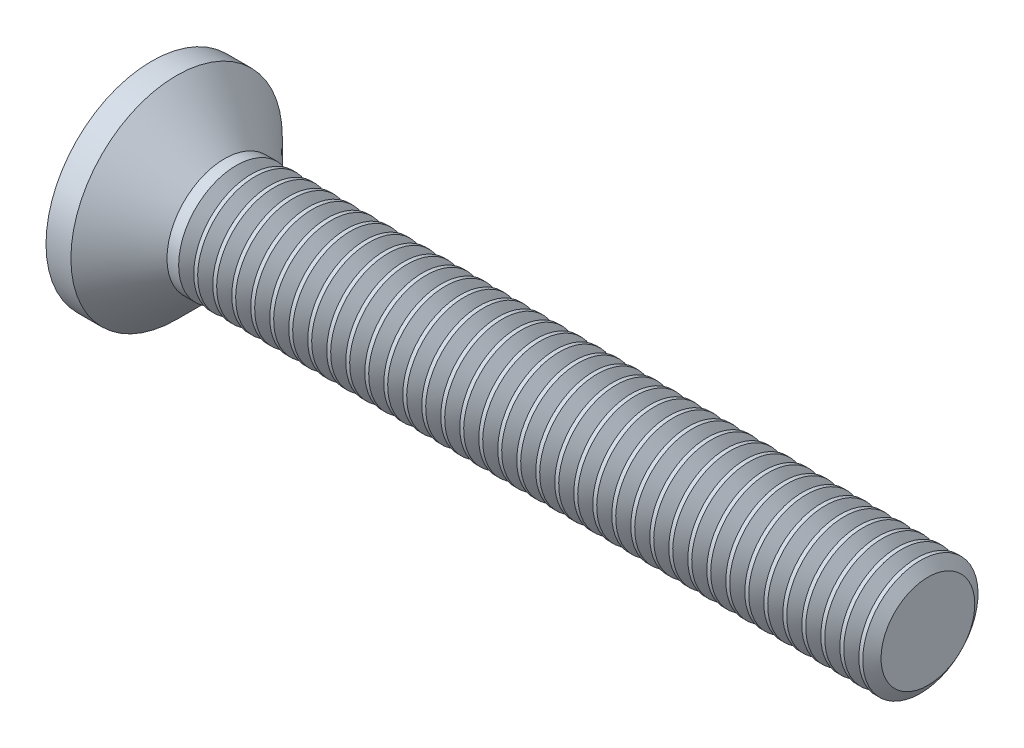
SolidWorks part; units mm, degrees
revolve "Base-Revolve" add sketch "BodySke" angle 360 about L4
sketch "BodySke" plane through (0, 0, 0) normal (0, 0, 1) x (1, 0, 0)
  line L0 (0, 0) -> (20.7277, 0)
  line L1 (20.7277, 0) -> (20.7277, 1.5)
  line L2 (20.7277, 1.5) -> (2.4277, 1.5)
  line L3 (2.4277, 1.5) -> (-7.1953, 11.123) construction
  line L4 (-15.875, 0) -> (82.55, 0) construction
  line L5 (2.4277, -1.5) -> (-7.1953, -11.123) construction
  line L6 (2.9277, 4.675) -> (2.9277, -11.2) construction
  line L7 (0.7277, 8.7375) -> (0.7277, -7.1375) construction
  line L8 (2.4277, 1.5) -> (1.1777, 2.75)
  line L9 (1.1777, 2.75) -> (0.53, 2.75)
  arc A0 (0, 0) -> (0.53, 2.75) centre (7.4, 0) cw
  arc A1 (0.7277, 3.2) -> (0, 0) centre (7.4, 0) ccw construction
  dimension "Crown_rad" = 7.4
  dimension "Diameter" = 3
  dimension "Advance" = 0.5
  dimension "Thread_nom" = 20
  dimension "Head_ang" = 90
  dimension "D3" = 6.4
  dimension "Side_ht" = 1.7
  dimension "D4" = 0.7277
  dimension "Length" = 20
  dimension "Head_dia" = 5.5
cosmetic thread "ThreadCosmetic" [suppressed] parameters "Thread_length"=17.8, "Thread_minor"=2.439
ref_plane "Plane1" through (0, 0, 0) normal (0, 0, 1) x (1, 0, 0)
ref_plane "Plane2" through (0, 0, 0) normal (0, 1, 0) x (1, 0, 0)
ref_plane "Plane3" through (0, 0, 0) normal (1, 0, 0) x (0, 0, -1)
sketch "Sketch2" plane through (0, 0, 0) normal (1, 0, 0) x (0, 0, -1)
  line L0 (2.75, -0.5) -> (-2.75, -0.5)
  line L1 (2.75, -0.5) -> (2.75, 0.5)
  line L2 (-2.75, 0.5) -> (2.75, 0.5)
  line L3 (-2.75, 0.5) -> (-2.75, -0.5)
  dimension "D1" = 5.5
  dimension "Slot_width" = 1
  dimension "D3" = 2.75
  dimension "D4" = 0.5
extrude "Slot" [suppressed] cut sketch "Sketch2" along normal blind 1.5
sketch "Sketch3" plane through (0, 0, 0) normal (1, 0, 0) x (0, 0, -1)
  line L0 (0.415, -1.72) -> (-0.415, -1.72)
  line L1 (0.415, -1.72) -> (0.415, 1.72)
  line L2 (-0.415, 1.72) -> (0.415, 1.72)
  line L3 (-0.415, 1.72) -> (-0.415, -1.72)
  dimension "Cross_width" = 0.83
  dimension "D1" = 0.415
  dimension "Cross_dia" = 3.44
  dimension "D2" = 1.72
ref_plane "Plane4" through (2.33, 0, 0) normal (1, 0, 0) x (0, 0, -1)
sketch "Sketch4" plane through (2.33, 0, 0) normal (1, 0, 0) x (0, 0, -1)
  line L0 (0.2075, -0.2075) -> (-0.2075, -0.2075)
  line L1 (0.2075, -0.2075) -> (0.2075, 0.2075)
  line L2 (-0.2075, 0.2075) -> (0.2075, 0.2075)
  line L3 (-0.2075, 0.2075) -> (-0.2075, -0.2075)
  dimension "D1" = 0.415
  dimension "D2" = 0.415
  dimension "D3" = 0.2075
  dimension "D4" = 0.2075
loft "Cross" cut profiles "Sketch3", "Sketch4"
pattern_circular "CirPattern1" count 2 every 90 about axis through (0, 0, 0) along (1, 0, 0) of "Cross"
sketch "ThdSchSke" plane through (0, 0, 0) normal (0, 0, 1) x (1, 0, 0)
  line L0 (2.9277, -1.2195) -> (2.7313, -1.5)
  line L1 (2.9277, -1.2195) -> (3.1241, -1.5)
  line L2 (3.1241, -1.5) -> (3.1241, -1.875)
  line L3 (-3.175, 0) -> (5.1513, 0) construction
  line L5 (3.1241, -1.875) -> (2.7313, -1.875)
  line L6 (2.7313, -1.875) -> (2.7313, -1.5)
  line L8 (20.7277, -1.5) -> (20.7277, 1.5) construction
  dimension "Diameter" = 3
  dimension "Thread_minor" = 2.439
  dimension "Start" = 17.8
revolve "ThreadSchematic" cut sketch "ThdSchSke" angle 360 about L3
pattern_linear "ThdSchPat" count 37 spacing 0.4944 along (1, 0, 0) of "ThreadSchematic"
equation "\"D1@Sketch2\" = \"Head_dia@BodySke\""
equation "\"D3@Sketch2\" = \"D1@Sketch2\" / 2"
equation "\"D4@Sketch2\" = \"Slot_width@Sketch2\" / 2"
equation "\"D1@Sketch3\" = \"Cross_width@Sketch3\" / 2"
equation "\"D2@Sketch3\" = \"Cross_dia@Sketch3\" / 2"
equation "\"D1@Sketch4\" = \"Cross_width@Sketch3\"*.5"
equation "\"D2@Sketch4\" = \"D1@Sketch4\""
equation "\"D3@Sketch4\" = \"D1@Sketch4\" / 2"
equation "\"D4@Sketch4\" = \"D2@Sketch4\" / 2"
equation "\"Thread_length@ThreadCosmetic\" = ((sgn( (\"Length@BodySke\" - \"Advance@BodySke\" - \"Side_ht@BodySke\" ) - \"Thread_nom@BodySke\" )-1)*( (\"Length@BodySke\" - \"Advance@BodySke\" - \"Side_ht@BodySke\" ) - \"Thread_nom@BodySke\" ))/-2+ \"Thread_nom@BodySke\""
equation "\"Thread_minor@ThdSchSke\" = \"Thread_minor@ThreadCosmetic\""
equation "\"Diameter@ThdSchSke\" = \"Diameter@BodySke\""
equation "\"Overcut@ThdSchSke\" = \"Diameter@BodySke\" * 1.25"
equation "\"Start@ThdSchSke\" =  \"Thread_length@ThreadCosmetic\""
equation "\"Num_threads@ThdSchPat\" = int( \"Thread_length@ThreadCosmetic\" / \"Advance@BodySke\" + 0.999 )  + 1"
equation "\"Advance@ThdSchPat\" = \"Thread_length@ThreadCosmetic\" /  (\"Num_threads@ThdSchPat\" - 1) 'relax it"
